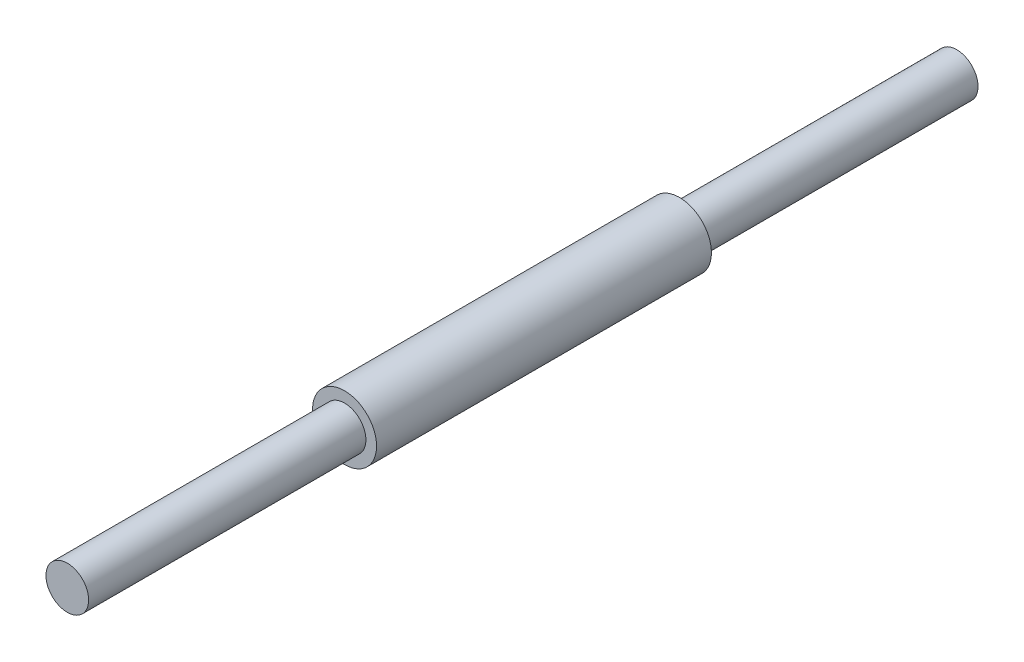
SolidWorks part; units mm, degrees
ref_plane "Front Plane" through (0, 0, 0) normal (0, 0, 1) x (1, 0, 0)
ref_plane "Top Plane" through (0, 0, 0) normal (0, 1, 0) x (1, 0, 0)
ref_plane "Right Plane" through (0, 0, 0) normal (1, 0, 0) x (0, 0, -1)
sketch "Sketch1" plane through (0, 0, 0) normal (0, 0, 1) x (1, 0, 0)
  circle A0 centre (0, 0) radius 3.81
  dimension "D1" = 7.62
extrude "Boss-Extrude1" add sketch "Sketch1" along normal blind 39.878
sketch "Sketch2" plane through (0, 0, 39.878) normal (0, 0, 1) x (1, 0, 0)
  circle A0 centre (0, 0) radius 2.54
  dimension "D1" = 5.08
extrude "Boss-Extrude2" add sketch "Sketch2" along normal blind 33.02
sketch "Sketch3" plane through (0, 0, 0) normal (0, 0, -1) x (-1, 0, 0)
  circle A0 centre (0, 0) radius 2.54
  dimension "D1" = 5.08
extrude "Boss-Extrude3" add sketch "Sketch3" along normal blind 33.02
